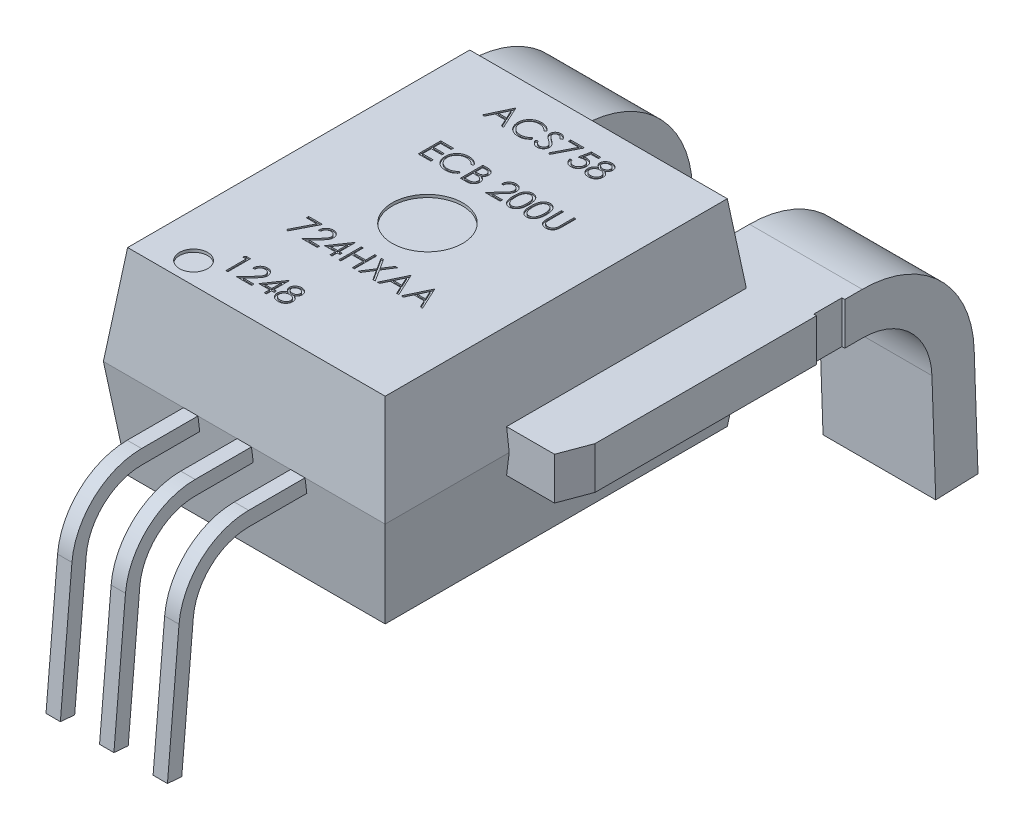
SolidWorks part; units mm, degrees
ref_plane "Front Plane" through (0, 0, 0) normal (0, 0, 1) x (1, 0, 0)
ref_plane "Top Plane" through (0, 0, 0) normal (0, 1, 0) x (1, 0, 0)
ref_plane "Right Plane" through (0, 0, 0) normal (1, 0, 0) x (0, 0, -1)
sketch "Sketch1" plane through (0, 0, 0) normal (0, 0, 1) x (1, 0, 0)
  line L0 (0, 0) -> (9.1405, 0)
  line L1 (9.1405, 0) -> (9.5703, 3.5)
  line L2 (9.5703, 3.5) -> (9.1405, 7)
  line L3 (9.1405, 7) -> (0, 7)
  line L4 (0, 7) -> (-0.4297, 3.5)
  line L5 (-0.4297, 3.5) -> (0, 0)
  line L6 (4.5703, 0) -> (4.5703, 7) construction
  line L7 (-0.4297, 3.5) -> (9.5703, 3.5) construction
  point P9 (4.802, 7)
  point P10 (4.5703, 3.5)
  point P11 (9.648, 3.5)
  point P12 (9.5694, 3.5)
  dimension "D1" = 7
  dimension "D2" = 10
  dimension "D3" = 7
  dimension "D4" = 7
extrude "Boss-Extrude1" add sketch "Sketch1" along normal blind 13
sketch "Sketch2" plane through (0, 0, 0) normal (1, 0, 0) x (0, 0, -1)
  line L0 (-13, 7) -> (-12.5703, 7)
  line L1 (-13, 7) -> (0, 7) construction
  line L2 (-12.5703, 7) -> (-13, 3.5)
  line L3 (-13, 3.5) -> (-13, 7)
  line L4 (-13, 3.5) -> (-13, 0)
  line L5 (-13, 0) -> (-12.5703, 0)
  line L6 (-13, 0) -> (0, 0) construction
  line L7 (-12.5703, 0) -> (-13, 3.5)
  line L8 (-6.5, 7) -> (-6.5, 0) construction
  line L9 (-0.4297, 0) -> (0, 3.5)
  line L10 (0, 0) -> (-0.4297, 0)
  line L11 (0, 3.5) -> (0, 0)
  line L12 (0, 3.5) -> (0, 7)
  line L13 (-0.4297, 7) -> (0, 3.5)
  line L14 (0, 7) -> (-0.4297, 7)
  dimension "D1" = 7
  dimension "D2" = 7
extrude "Cut-Extrude1" cut sketch "Sketch2" against normal through all both and the other way through all contours L5 L7 L4 | L3 L2 L0 | L12 L14 L13 | L11 L10 L9
sketch "Sketch3" plane through (0, 7, 0) normal (0, 1, 0) x (1, 0, 0)
  line L0 (0, -0.4297) -> (9.1405, -12.5703) construction
  line L1 (-0.4297, -13) -> (-0.4297, 0) construction
  line L2 (-0.4297, -13) -> (9.5703, -13) construction
  circle A0 centre (4.5703, -6.5) radius 1.25
  circle A1 centre (1.5703, -11.8) radius 0.5
  point P8 (1.4163, -11.8822)
  point P9 (1.5339, -11.6619)
  point P10 (1.6727, -11.7313)
  dimension "D1" = 2.5
  dimension "D2" = 1
  dimension "D3" = 2
  dimension "D4" = 1.2
extrude "Cut-Extrude2" cut sketch "Sketch3" against normal blind 0.1
ref_plane "Plane1" through (0, 3.5, 0) normal (0, -1, 0) x (-1, 0, 0)
sketch "Sketch4" plane through (0, 3.5, 0) normal (0, -1, 0) x (-1, 0, 0)
  line L0 (-1.5703, -8.6) -> (2.0383, -8.6)
  line L1 (2.0383, -8.6) -> (2.4297, -7.5499)
  line L2 (2.4297, -7.5499) -> (2.4297, 0.3089)
  line L3 (2.4297, 0.3089) -> (2.3297, 0.3089)
  line L4 (2.3297, 0.3089) -> (2.3297, 1.3089)
  line L5 (2.3297, 1.3089) -> (2.4297, 1.3089)
  line L6 (2.4297, 1.3089) -> (2.4297, 1.9297)
  line L7 (2.4297, 1.9297) -> (-1.5703, 1.9297)
  line L8 (-1.5703, 1.9297) -> (-1.5703, -8.6)
  line L9 (0.4297, -13) -> (-9.5703, -13) construction
  line L10 (-4.5703, 14.0642) -> (-4.5703, -14.9237) construction
  line L11 (-7.5703, 1.9297) -> (-7.5703, -8.6)
  line L12 (-11.5703, 1.9297) -> (-7.5703, 1.9297)
  line L13 (-11.5703, 1.3089) -> (-11.5703, 1.9297)
  line L14 (-11.4703, 1.3089) -> (-11.5703, 1.3089)
  line L15 (-11.4703, 0.3089) -> (-11.4703, 1.3089)
  line L16 (-11.5703, 0.3089) -> (-11.4703, 0.3089)
  line L17 (-11.5703, -7.5499) -> (-11.5703, 0.3089)
  line L18 (-11.1789, -8.6) -> (-11.5703, -7.5499)
  line L19 (-7.5703, -8.6) -> (-11.1789, -8.6)
  line L20 (0, -0.4297) -> (-9.1405, -0.4297) construction
  point P2 (0, 0)
  point P14 (1.9453, 0.3089)
  point P24 (2.3815, -8.6)
  point P27 (-4.5703, -0.4297)
  point P28 (-11.1789, -8.6)
  dimension "D1" = 4
  dimension "D2" = 4.4
  dimension "D3" = 0.1
  dimension "D4" = 1
  dimension "D5" = 14
extrude "Boss-Extrude2" add sketch "Sketch4" along normal blind 0.75 and the other way blind 0.75
sketch "Sketch5" plane through (11.5703, 0, 0) normal (1, 0, 0) x (0, 0, -1)
  line L0 (1.3089, 4.25) -> (1.9297, 4.25)
  line L2 (1.9297, 2.75) -> (1.3089, 2.75)
  line L3 (1.3089, 2.75) -> (1.3089, 4.25)
  line L5 (5.9012, 0.4147) -> (6.037, -3.4738)
  line L6 (6.037, -3.4738) -> (4.5379, -3.5262)
  line L7 (4.5379, -3.5262) -> (4.4022, 0.3623)
  line L8 (-12.5703, 0) -> (-0.4297, 0) construction
  arc A0 (1.9297, 4.25) -> (5.9012, 0.4147) centre (1.9297, 0.276) cw
  arc A1 (4.4022, 0.3623) -> (1.9297, 2.75) centre (1.9297, 0.276) ccw
  point P10 (4.5592, -4.1336)
  point P17 (5.2875, -3.5)
  dimension "D1" = 1.5
  dimension "D3" = 3.5
extrude "Boss-Extrude3" add sketch "Sketch5" against normal up to surface (4 mm away) up to face at (7.5703, 3.5, -0.735)
sketch "Sketch6" plane through (-2.4297, 0, 0) normal (-1, 0, 0) x (0, 0, 1)
  line L0 (-1.9297, 4.25) -> (-1.9297, 2.75) construction
  line L1 (-4.5379, -3.5262) -> (-6.037, -3.4738) construction
  line L2 (-6.037, -3.4738) -> (-5.9012, 0.4147) construction
  line L3 (-4.4022, 0.3623) -> (-4.5379, -3.5262) construction
  line L4 (-1.9297, 4.25) -> (-1.9297, 2.75)
  line L5 (-4.5379, -3.5262) -> (-6.037, -3.4738)
  line L6 (-6.037, -3.4738) -> (-5.9012, 0.4147)
  line L7 (-4.4022, 0.3623) -> (-4.5379, -3.5262)
  arc A0 (-1.9297, 2.75) -> (-4.4022, 0.3623) centre (-1.9297, 0.276) ccw construction
  arc A1 (-1.9297, 4.25) -> (-5.9012, 0.4147) centre (-1.9297, 0.276) ccw construction
  arc A2 (-1.9297, 2.75) -> (-4.4022, 0.3623) centre (-1.9297, 0.276) ccw
  arc A3 (-1.9297, 4.25) -> (-5.9012, 0.4147) centre (-1.9297, 0.276) ccw
extrude "Boss-Extrude4" add sketch "Sketch6" against normal up to surface (4 mm away) up to face at (1.5703, 3.5, -0.735)
sketch "Sketch7" plane through (0, 3.5, 0) normal (0, -1, 0) x (-1, 0, 0)
  line L0 (-4.5703, -13) -> (-4.5703, -15) construction
  line L1 (0.4297, -13) -> (-9.5703, -13) construction
  line L2 (-6.4703, -13) -> (-6.4703, -15) construction
  line L3 (-2.6703, -13) -> (-2.6703, -15) construction
  line L5 (-2.4153, -15) -> (-2.9253, -15)
  line L6 (-2.4153, -15) -> (-2.4153, -12.7926)
  line L7 (-2.4153, -12.7926) -> (-2.9253, -12.7926)
  line L8 (-2.9253, -15) -> (-2.9253, -12.7926)
  line L9 (-4.3153, -15) -> (-4.8253, -15)
  line L10 (-4.3153, -15) -> (-4.3153, -12.7926)
  line L11 (-4.3153, -12.7926) -> (-4.8253, -12.7926)
  line L12 (-4.8253, -15) -> (-4.8253, -12.7926)
  line L13 (-6.2153, -15) -> (-6.7253, -15)
  line L14 (-6.2153, -15) -> (-6.2153, -12.7926)
  line L15 (-6.2153, -12.7926) -> (-6.7253, -12.7926)
  line L16 (-6.7253, -15) -> (-6.7253, -12.7926)
  dimension "D1" = 1.9
  dimension "D2" = 1.9
  dimension "D3" = 2
  dimension "D4" = 0.51
extrude "Boss-Extrude5" add sketch "Sketch7" along normal blind 0.51
sketch "Sketch8" plane through (6.7253, 0, 0) normal (1, 0, 0) x (0, 0, -1)
  line L1 (-12.9374, 2.99) -> (-15, 2.99) construction
  line L2 (-15, 2.99) -> (-15, 3.5) construction
  line L4 (-16.9634, 1.1909) -> (-17.3738, -3.5)
  line L5 (-17.3738, -3.5) -> (-17.8818, -3.4556)
  line L6 (-17.8818, -3.4556) -> (-17.4714, 1.2354)
  line L7 (-12.5703, 0) -> (-0.4297, 0) construction
  line L8 (-15, 3.5) -> (-14.7584, 3.5)
  line L9 (-13, 3.5) -> (-15, 3.5) construction
  line L10 (-14.7584, 3.5) -> (-14.7584, 2.99)
  line L11 (-14.7584, 2.99) -> (-15, 2.99)
  arc A0 (-15, 2.99) -> (-16.9634, 1.1909) centre (-15, 1.0191) ccw
  arc A1 (-17.4714, 1.2354) -> (-15, 3.5) centre (-15, 1.0191) cw
  dimension "D1" = 0.51
  dimension "D2" = 0.51
  dimension "D3" = 5
  dimension "D4" = 3.5
extrude "Boss-Extrude6" add sketch "Sketch8" against normal up to surface (0.51 mm away) up to face at (6.2153, 3.245, 13.9843)
sketch "Sketch9" plane through (4.8253, 0, 0) normal (1, 0, 0) x (0, 0, -1)
  line L0 (-17.3738, -3.5) -> (-17.8818, -3.4556) construction
  line L1 (-17.8818, -3.4556) -> (-17.4714, 1.2354) construction
  line L2 (-16.9634, 1.1909) -> (-17.3738, -3.5) construction
  line L3 (-17.3738, -3.5) -> (-17.8818, -3.4556)
  line L4 (-17.8818, -3.4556) -> (-17.4714, 1.2354)
  line L5 (-16.9634, 1.1909) -> (-17.3738, -3.5)
  line L6 (-15, 2.99) -> (-15, 3.5) construction
  line L7 (-15, 2.99) -> (-15, 3.5)
  arc A0 (-15, 2.99) -> (-16.9634, 1.1909) centre (-15, 1.0191) ccw construction
  arc A1 (-15, 3.5) -> (-17.4714, 1.2354) centre (-15, 1.0191) ccw construction
  arc A2 (-15, 2.99) -> (-16.9634, 1.1909) centre (-15, 1.0191) ccw
  arc A3 (-15, 3.5) -> (-17.4714, 1.2354) centre (-15, 1.0191) ccw
extrude "Boss-Extrude7" add sketch "Sketch9" against normal up to surface (0.51 mm away) up to face at (4.3153, 3.245, 13.9843)
sketch "Sketch10" plane through (2.9253, 0, 0) normal (1, 0, 0) x (0, 0, -1)
  line L0 (-15, 2.99) -> (-15, 3.5) construction
  line L1 (-17.3738, -3.5) -> (-17.8818, -3.4556) construction
  line L2 (-17.8818, -3.4556) -> (-17.4714, 1.2354) construction
  line L3 (-16.9634, 1.1909) -> (-17.3738, -3.5) construction
  line L4 (-15, 2.99) -> (-15, 3.5)
  line L5 (-17.3738, -3.5) -> (-17.8818, -3.4556)
  line L6 (-17.8818, -3.4556) -> (-17.4714, 1.2354)
  line L7 (-16.9634, 1.1909) -> (-17.3738, -3.5)
  arc A0 (-15, 2.99) -> (-16.9634, 1.1909) centre (-15, 1.0191) ccw construction
  arc A1 (-15, 3.5) -> (-17.4714, 1.2354) centre (-15, 1.0191) ccw construction
  arc A2 (-15, 2.99) -> (-16.9634, 1.1909) centre (-15, 1.0191) ccw
  arc A3 (-15, 3.5) -> (-17.4714, 1.2354) centre (-15, 1.0191) ccw
extrude "Boss-Extrude8" add sketch "Sketch10" against normal up to surface (0.51 mm away) up to face at (2.4153, 3.245, 13.9843)
sketch "Sketch12" plane through (0, 7, 0) normal (0, 1, 0) x (1, 0, 0)
  text T0 "ACS758\r\nECB 200U\r\n\r\n724HXAA\r\n1248" font "Century Gothic" height 0.8
extrude "Cut-Extrude3" cut sketch "Sketch12" against normal blind 0.05
